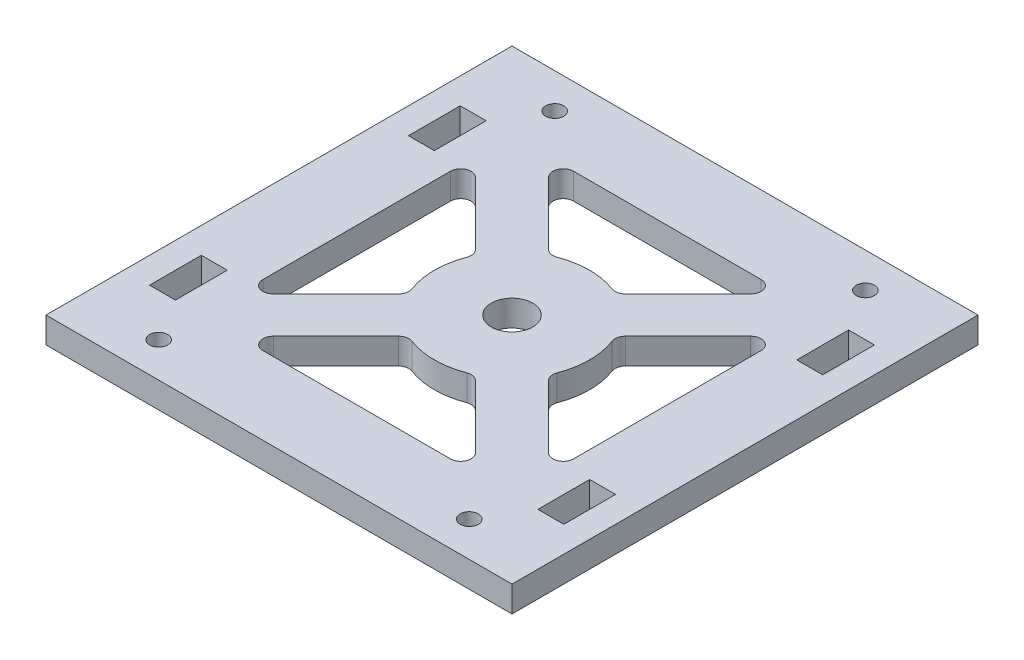
SolidWorks part; units mm, degrees
ref_plane "Front Plane" through (0, 0, 0) normal (0, 0, 1) x (1, 0, 0)
ref_plane "Top Plane" through (0, 0, 0) normal (0, 1, 0) x (1, 0, 0)
ref_plane "Right Plane" through (0, 0, 0) normal (1, 0, 0) x (0, 0, -1)
sketch "Sketch1" plane through (0, 0, 0) normal (0, 1, 0) x (1, 0, 0)
  line L0 (-26.5858, 19.5147) -> (-14.49, 7.4189)
  line L5 (-45, 45) -> (45, 45)
  line L6 (-45, 45) -> (-45, -45)
  line L11 (-45, -45) -> (45, -45)
  line L20 (45, 45) -> (45, -45)
  line L21 (-45, 45) -> (45, -45) construction
  line L23 (-45, -45) -> (45, 45) construction
  line L55 (-18.1005, 30) -> (18.1005, 30)
  line L60 (-30, 18.1005) -> (-30, -18.1005)
  line L61 (-30, -30) -> (0, -30) construction
  line L62 (30, 0) -> (30, -30) construction
  line L63 (-30, 30) -> (30, -30) construction
  line L64 (-30, -30) -> (30, 30) construction
  line L65 (-19.5147, 26.5858) -> (-7.4189, 14.49)
  line L66 (-30, 30) -> (-30, 22.9289) construction
  line L67 (-30, 30) -> (-22.9289, 30) construction
  line L68 (-1000, 0) -> (49000, 0) construction
  line L69 (0, -1000) -> (0, 49000) construction
  line L70 (0, 30) -> (30, 30) construction
  line L71 (30, 30) -> (30, -30) construction
  line L72 (0, -30) -> (30, -30) construction
  line L73 (-30, 0) -> (-30, -30) construction
  line L74 (30, 30) -> (22.9289, 30) construction
  line L75 (30, 30) -> (30, 22.9289) construction
  line L76 (19.5147, 26.5858) -> (7.4189, 14.49)
  line L77 (30, 18.1005) -> (30, -18.1005)
  line L78 (26.5858, 19.5147) -> (14.49, 7.4189)
  line L79 (30, -30) -> (30, -22.9289) construction
  line L80 (30, -30) -> (22.9289, -30) construction
  line L81 (0, -30) -> (30, -30) construction
  line L82 (-30, -30) -> (-22.9289, -30) construction
  line L83 (-30, -30) -> (-30, -22.9289) construction
  line L84 (26.5858, -19.5147) -> (14.49, -7.4189)
  line L85 (19.5147, -26.5858) -> (7.4189, -14.49)
  line L86 (-19.5147, -26.5858) -> (-7.4189, -14.49)
  line L87 (-18.1005, -30) -> (18.1005, -30)
  line L88 (-26.5858, -19.5147) -> (-14.49, -7.4189)
  circle A0 centre (0, 0) radius 3.5013
  arc A1 (-14.0331, 5.2983) -> (-14.0331, -5.2983) centre (0, 0) ccw
  arc A2 (-6.4645, 13.5355) -> (-10.6066, 10.6066) centre (0, 0) ccw construction
  arc A3 (-10.6066, 10.6066) -> (-13.5355, 6.4645) centre (0, 0) ccw construction
  arc A4 (-5.2983, 14.0331) -> (-7.4189, 14.49) centre (-6.0047, 15.9042) cw
  arc A5 (-14.0331, 5.2983) -> (-14.49, 7.4189) centre (-15.9042, 6.0047) ccw
  arc A6 (-26.5858, 19.5147) -> (-30, 18.1005) centre (-28, 18.1005) ccw
  arc A7 (-18.1005, 30) -> (-19.5147, 26.5858) centre (-18.1005, 28) ccw
  arc A8 (-15, 0) -> (-10.6066, -10.6066) centre (0, 0) ccw construction
  arc A9 (5.2983, 14.0331) -> (-5.2983, 14.0331) centre (0, 0) ccw
  arc A10 (-10.6066, -10.6066) -> (0, -15) centre (0, 0) ccw construction
  arc A11 (0, -15) -> (10.6066, -10.6066) centre (0, 0) ccw construction
  arc A12 (10.6066, -10.6066) -> (15, 0) centre (0, 0) ccw construction
  arc A13 (10.6066, -10.6066) -> (10.6066, 10.6066) centre (0, 0) ccw construction
  arc A14 (10.6066, 10.6066) -> (0, 15) centre (0, 0) ccw construction
  arc A15 (10.6066, 10.6066) -> (13.5355, 6.4645) centre (0, 0) cw construction
  arc A16 (6.4645, 13.5355) -> (10.6066, 10.6066) centre (0, 0) cw construction
  arc A17 (18.1005, 30) -> (19.5147, 26.5858) centre (18.1005, 28) cw
  arc A18 (26.5858, 19.5147) -> (30, 18.1005) centre (28, 18.1005) cw
  arc A19 (14.0331, 5.2983) -> (14.49, 7.4189) centre (15.9042, 6.0047) cw
  arc A20 (5.2983, 14.0331) -> (7.4189, 14.49) centre (6.0047, 15.9042) ccw
  arc A21 (14.0331, 5.2983) -> (14.0331, -5.2983) centre (0, 0) cw
  arc A22 (6.4645, -13.5355) -> (10.6066, -10.6066) centre (0, 0) ccw construction
  arc A23 (10.6066, -10.6066) -> (13.5355, -6.4645) centre (0, 0) ccw construction
  arc A24 (10.6066, -10.6066) -> (0, -15) centre (0, 0) cw construction
  arc A25 (-10.6066, -10.6066) -> (-13.5355, -6.4645) centre (0, 0) cw construction
  arc A26 (-6.4645, -13.5355) -> (-10.6066, -10.6066) centre (0, 0) cw construction
  arc A27 (5.2983, -14.0331) -> (7.4189, -14.49) centre (6.0047, -15.9042) cw
  arc A28 (14.0331, -5.2983) -> (14.49, -7.4189) centre (15.9042, -6.0047) ccw
  arc A29 (26.5858, -19.5147) -> (30, -18.1005) centre (28, -18.1005) ccw
  arc A30 (18.1005, -30) -> (19.5147, -26.5858) centre (18.1005, -28) ccw
  arc A31 (5.2983, -14.0331) -> (-5.2983, -14.0331) centre (0, 0) cw
  arc A32 (-18.1005, -30) -> (-19.5147, -26.5858) centre (-18.1005, -28) cw
  arc A33 (-26.5858, -19.5147) -> (-30, -18.1005) centre (-28, -18.1005) cw
  arc A34 (-14.0331, -5.2983) -> (-14.49, -7.4189) centre (-15.9042, -6.0047) cw
  arc A35 (-5.2983, -14.0331) -> (-7.4189, -14.49) centre (-6.0047, -15.9042) ccw
  point P0 (0, 0)
  dimension "D3" = 30
  dimension "D4" = 7.0027
  dimension "D8" = 2
  dimension "D1" = 90
  dimension "D2" = 90
  dimension "D5" = 15
  dimension "D6" = 15
  dimension "D7" = 5
extrude "Boss-Extrude1" add sketch "Sketch1" along normal blind 5
sketch "Sketch2" plane through (0, 5, 0) normal (0, 1, 0) x (1, 0, 0)
  line L0 (-998.1413, -40) -> (49001.8587, -40) construction
  line L1 (0, -1000) -> (0, 49000) construction
  line L2 (-1000, 0) -> (49000, 0) construction
  line L3 (-45, -45) -> (45, -45) construction
  line L4 (40, 30) -> (35, 30)
  line L5 (-40, -1027.013) -> (-40, 48972.987) construction
  line L6 (-45, 45) -> (-45, -45) construction
  line L7 (35, -30) -> (35, -20)
  line L8 (-40, -30) -> (-35, -30)
  line L9 (-40, -30) -> (-40, -20)
  line L10 (-40, -20) -> (-35, -20)
  line L11 (-35, -30) -> (-35, -20)
  line L12 (40, -20) -> (35, -20)
  line L13 (40, -30) -> (40, -20)
  line L14 (40, -30) -> (35, -30)
  line L15 (40, 30) -> (40, 20)
  line L16 (40, 20) -> (35, 20)
  line L17 (35, 30) -> (35, 20)
  line L18 (-35, 30) -> (-35, 20)
  line L19 (-40, 20) -> (-35, 20)
  line L20 (-40, 30) -> (-40, 20)
  line L21 (-40, 30) -> (-35, 30)
  circle A0 centre (-30, -38.25) radius 1.75
  circle A1 centre (30, -38.25) radius 1.75
  circle A2 centre (30, 38.25) radius 1.75
  circle A3 centre (-30, 38.25) radius 1.75
  dimension "D2" = 3.5
  dimension "D1" = 5
  dimension "D3" = 30
  dimension "D4" = 5
  dimension "D5" = 20
  dimension "D6" = 5
  dimension "D7" = 10
extrude "Cut-Extrude1" cut sketch "Sketch2" against normal through all both and the other way through all
sketch "Sketch3" plane through (0, 5, 0) normal (0, 1, 0) x (1, 0, 0)
  circle A1 centre (0, 0) radius 4
extrude "Cut-Extrude2" cut sketch "Sketch3" against normal blind 10
